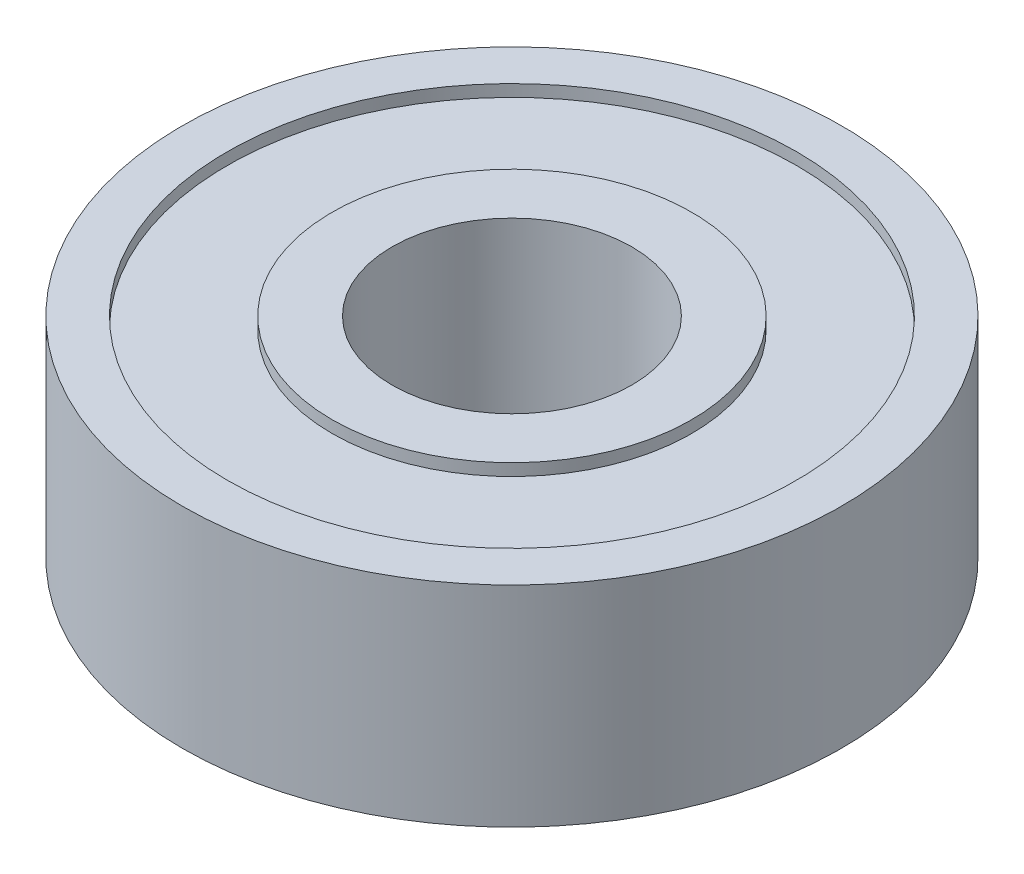
SolidWorks part; units mm, degrees
ref_plane "Front" through (0, 0, 0) normal (0, 0, 1) x (1, 0, 0)
ref_plane "Top" through (0, 0, 0) normal (0, 1, 0) x (1, 0, 0)
ref_plane "Right" through (0, 0, 0) normal (1, 0, 0) x (0, 0, -1)
sketch "草圖1" plane through (0, 0, 0) normal (0, 1, 0) x (1, 0, 0)
  circle A0 centre (0, 0) radius 4
  circle A1 centre (0, 0) radius 11
  dimension "D1" = 8
  dimension "D2" = 22
extrude "填料-伸長1" add sketch "草圖1" along normal mid plane 7
sketch "草圖2" plane through (0, 0, 0) normal (0, 1, 0) x (1, 0, 0)
  circle A0 centre (0, 0) radius 6
  circle A1 centre (0, 0) radius 9.5
  dimension "D1" = 12
  dimension "D2" = 19
extrude "除料-伸長1" cut sketch "草圖2" against normal blind 0.4 from surface at 3.5 starting at face at (0, 3.5, 11)
mirror "鏡射4" about plane through (0, 0, 0) normal (0, 1, 0) of "除料-伸長1"
